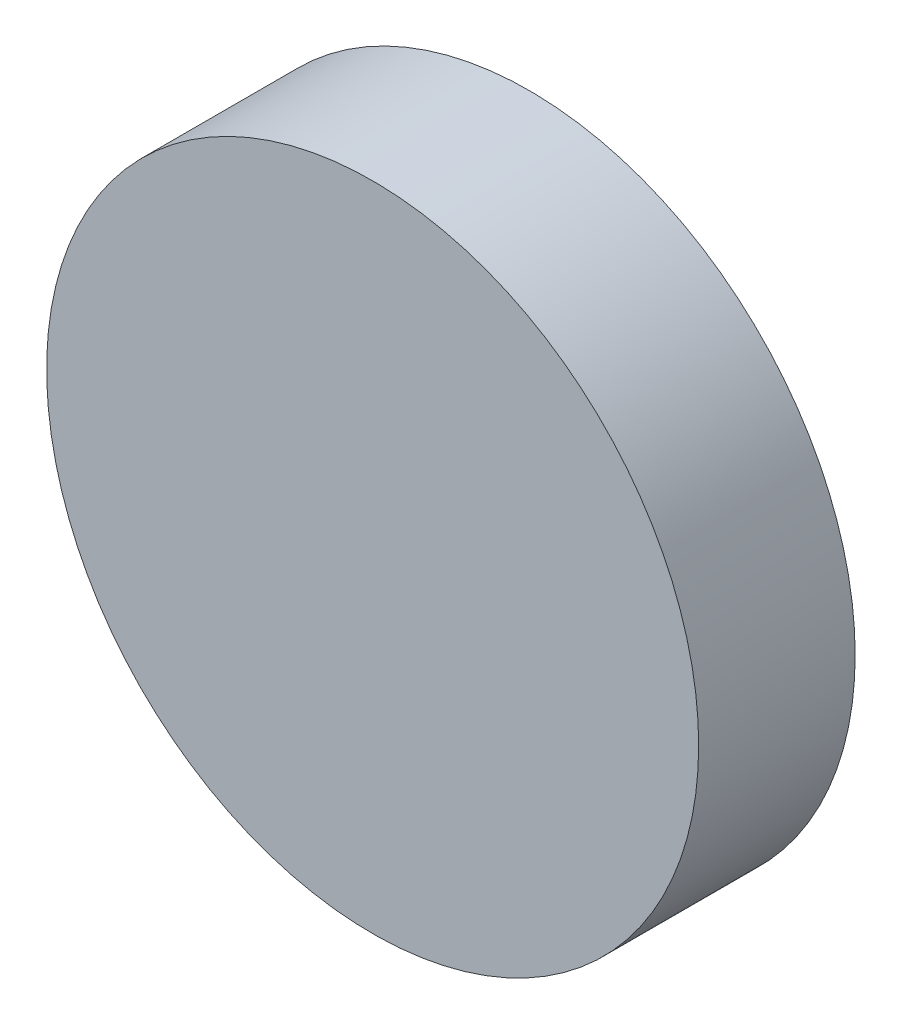
SolidWorks part; units mm, degrees
ref_plane "前视基准面" through (0, 0, 0) normal (0, 0, 1) x (1, 0, 0)
ref_plane "上视基准面" through (0, 0, 0) normal (0, 1, 0) x (1, 0, 0)
ref_plane "右视基准面" through (0, 0, 0) normal (1, 0, 0) x (0, 0, -1)
sketch "草图1" plane through (0, 0, 0) normal (0, 0, 1) x (1, 0, 0)
  circle A0 centre (0, 0) radius 6.25
  dimension "D1" = 12.5
extrude "凸台-拉伸1" add sketch "草图1" along normal blind 3
